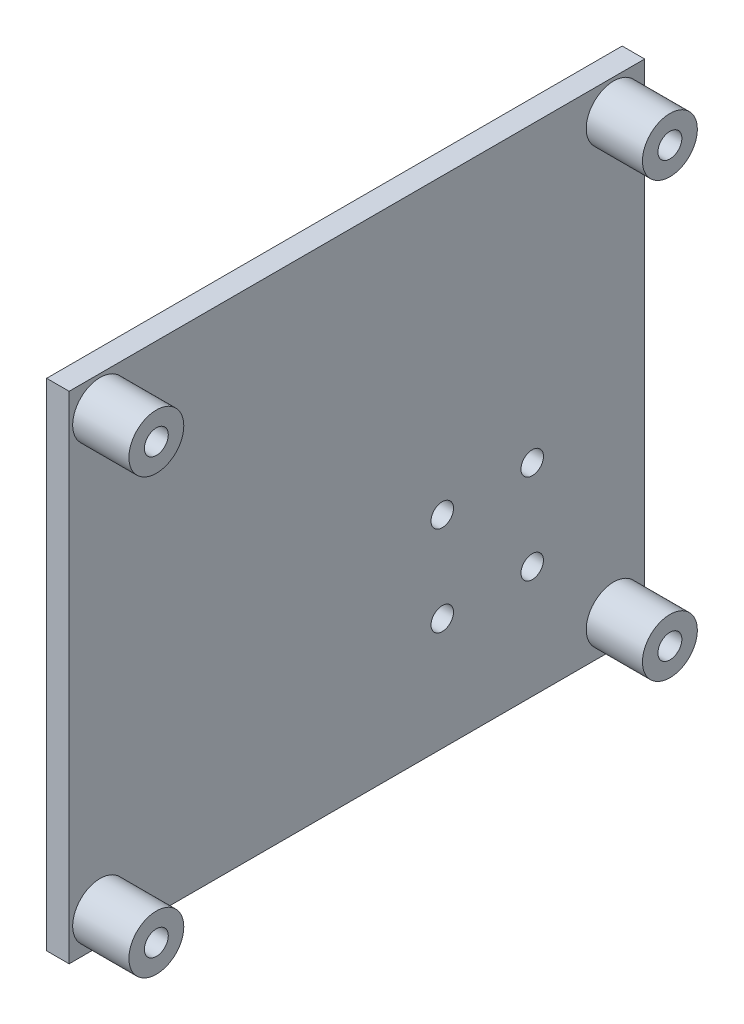
SolidWorks part; units mm, degrees
ref_plane "Front Plane" through (0, 0, 0) normal (0, 0, 1) x (1, 0, 0)
ref_plane "Top Plane" through (0, 0, 0) normal (0, 1, 0) x (1, 0, 0)
ref_plane "Right Plane" through (0, 0, 0) normal (1, 0, 0) x (0, 0, -1)
sketch "Sketch1" plane through (0, 0, 0) normal (1, 0, 0) x (0, 0, -1)
  line L1 (-336.1032, 94.3768) -> (-271.1032, 94.3768)
  line L2 (-336.1032, 94.3768) -> (-336.1032, 38.3768)
  line L3 (-336.1032, 38.3768) -> (-271.1032, 38.3768)
  line L4 (-271.1032, 94.3768) -> (-271.1032, 38.3768)
  dimension "D1" = 65
  dimension "D2" = 56
extrude "Boss-Extrude1" add sketch "Sketch1" along normal blind 2.54
sketch "Sketch2" plane through (2.54, 0, 0) normal (1, 0, 0) x (0, 0, -1)
  line L0 (-336.1032, 38.3768) -> (-271.1032, 38.3768) construction
  line L1 (-336.1032, 94.3768) -> (-336.1032, 38.3768) construction
  circle A0 centre (-332.6032, 90.8768) radius 1.35
  circle A1 centre (-274.6032, 90.8768) radius 1.35
  circle A2 centre (-332.6032, 41.8768) radius 1.35
  circle A3 centre (-274.6032, 41.8768) radius 1.35
  circle A4 centre (-332.6032, 90.8768) radius 3.1
  circle A5 centre (-274.6032, 90.8768) radius 3.1
  circle A6 centre (-274.6032, 41.8768) radius 3.1
  circle A7 centre (-332.6032, 41.8768) radius 3.1
  dimension "D1" = 2.7
  dimension "D2" = 2.7
  dimension "D3" = 2.7
  dimension "D4" = 2.7
  dimension "D5" = 6.2
  dimension "D6" = 6.2
  dimension "D7" = 6.2
  dimension "D8" = 6.2
  dimension "D9" = 58
  dimension "D10" = 0
  dimension "D11" = 49
  dimension "D12" = 3.5
  dimension "D13" = 3.5
  dimension "D14" = 0
extrude "Boss-Extrude2" add sketch "Sketch2" along normal blind 6.35
sketch "Sketch3" plane through (0, 0, 0) normal (-1, 0, 0) x (0, 0, 1)
  line L0 (271.1032, 38.3768) -> (271.1032, 94.3768) construction
  line L1 (336.1032, 38.3768) -> (271.1032, 38.3768) construction
  circle A0 centre (283.8032, 61.2368) radius 1.27
  circle A1 centre (293.9632, 61.2368) radius 1.27
  circle A2 centre (283.8032, 51.0768) radius 1.27
  circle A3 centre (293.9632, 51.0768) radius 1.27
  circle A4 centre (283.8032, 61.2368) radius 2.54
  circle A5 centre (293.9632, 61.2368) radius 2.54
  circle A6 centre (283.8032, 51.0768) radius 2.54
  circle A7 centre (293.9632, 51.0768) radius 2.54
  dimension "D1" = 2.54
  dimension "D2" = 2.54
  dimension "D3" = 2.54
  dimension "D4" = 2.54
  dimension "D5" = 5.08
  dimension "D6" = 5.08
  dimension "D7" = 5.08
  dimension "D8" = 5.08
  dimension "D9" = 10.16
  dimension "D10" = 0
  dimension "D11" = 12.7
  dimension "D12" = 0
  dimension "D13" = 10.16
  dimension "D14" = 12.7
extrude "Boss-Extrude3" add sketch "Sketch3" along normal blind 6.35
sketch "Sketch4" plane through (2.54, 0, 0) normal (1, 0, 0) x (0, 0, -1)
  circle A0 centre (-332.6032, 90.8768) radius 1.35
  circle A1 centre (-274.6032, 90.8768) radius 1.35
  circle A2 centre (-274.6032, 41.8768) radius 1.35
  circle A3 centre (-332.6032, 41.8768) radius 1.35
  circle A4 centre (-283.8032, 61.2368) radius 1.27
  circle A5 centre (-293.9632, 61.2368) radius 1.27
  circle A6 centre (-283.8032, 51.0768) radius 1.27
  circle A7 centre (-293.9632, 51.0768) radius 1.27
extrude "Cut-Extrude1" cut sketch "Sketch4" against normal mid plane 25.4
